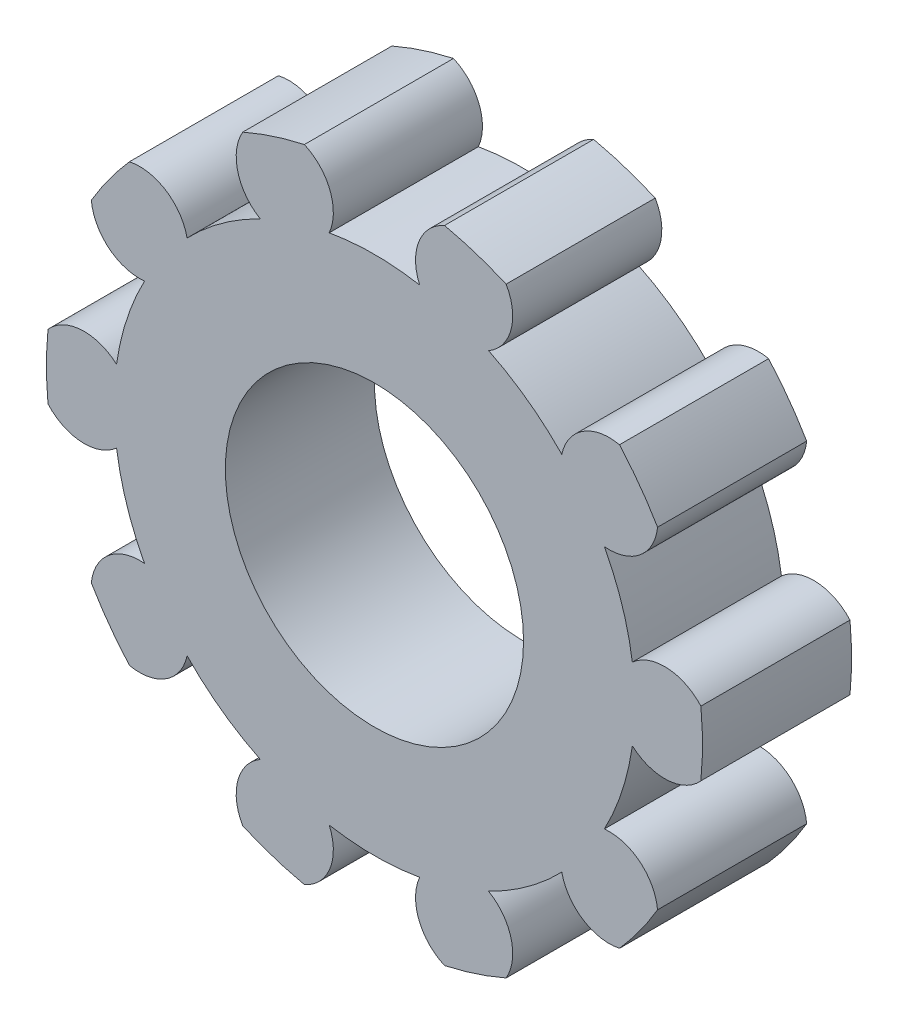
SolidWorks part; units mm, degrees
ref_plane "Front Plane" through (0, 0, 0) normal (0, 0, 1) x (1, 0, 0)
ref_plane "Top Plane" through (0, 0, 0) normal (0, 1, 0) x (1, 0, 0)
ref_plane "Right Plane" through (0, 0, 0) normal (1, 0, 0) x (0, 0, -1)
sketch "Sketch1" plane through (0, 0, 0) normal (0, 0, 1) x (1, 0, 0)
  circle A0 centre (0, 0) radius 6
  circle A1 centre (0, 0) radius 13.2
extrude "Boss-Extrude1" add sketch "Sketch1" along normal blind 6
sketch "Sketch2" plane through (0, 0, 6) normal (0, 0, 1) x (1, 0, 0)
  line L0 (0, 0) -> (0, 15.2) construction
  line L1 (-1.8199, 15.2) -> (0, 0) construction
  line L2 (1.8199, 15.2) -> (0, 0) construction
  arc A0 (-1.8199, 12) -> (1.8199, 12) centre (0, 0) cw
  arc A1 (-2.8199, 12.8953) -> (2.8199, 12.8953) centre (0, 0) cw
  arc A2 (-1.8199, 10.32) -> (1.8199, 10.32) centre (0, 0) cw
  arc A3 (-2.8199, 12.8953) -> (-1.8199, 10.32) centre (-3.6075, 11.1076) cw
  arc A4 (2.8199, 12.8953) -> (1.8199, 10.32) centre (3.6075, 11.1076) ccw
extrude "Cut-Extrude1" cut sketch "Sketch2" against normal through all contours A1 A4 A2 A3
pattern_circular "CirPattern1" count 10 over 360 about axis through (0, 0, 0) along (0, 0, 1) of "Cut-Extrude1"
